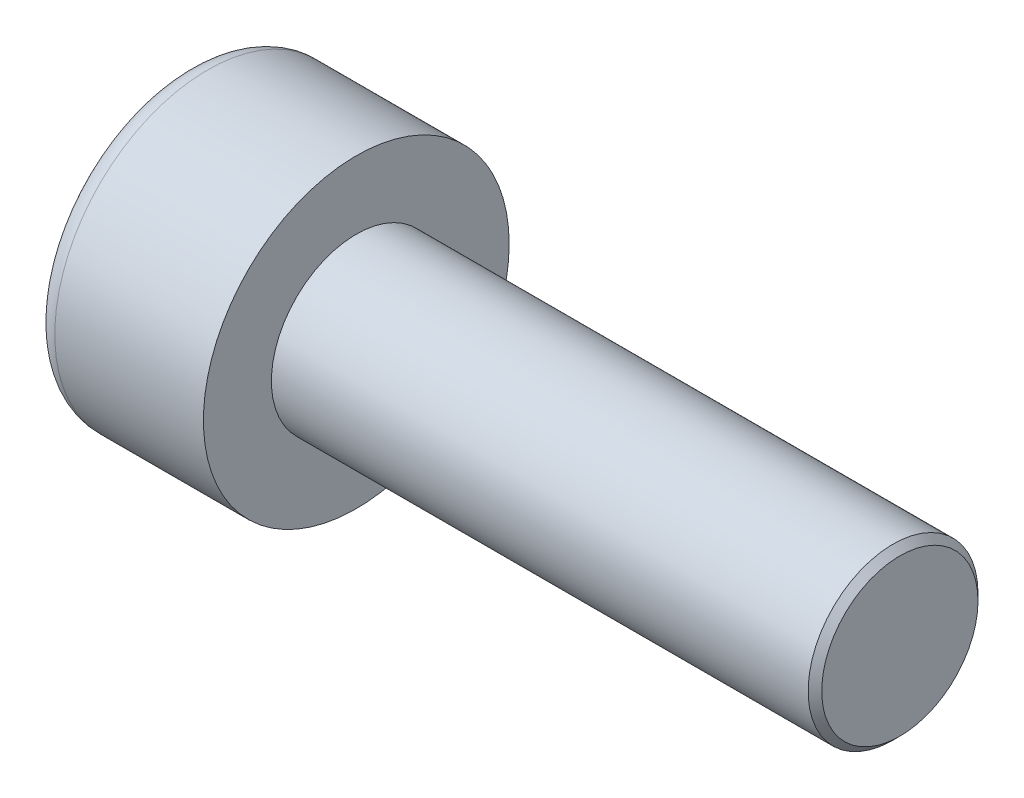
SolidWorks part; units mm, degrees
ref_plane "Front" through (0, 0, 0) normal (0, 0, 1) x (1, 0, 0)
ref_plane "Top" through (0, 0, 0) normal (0, 1, 0) x (1, 0, 0)
ref_plane "Right" through (0, 0, 0) normal (1, 0, 0) x (0, 0, -1)
sketch "Sketch1" plane through (0, 0, 0) normal (1, 0, 0) x (0, 0, -1)
  circle A0 centre (0, 0) radius 2.25
  dimension "dk" = 4.5
extrude "BaseHead" add sketch "Sketch1" along normal blind 2.5
sketch "Sketch2" plane through (2.5, 0, 0) normal (1, 0, 0) x (0, 0, -1)
  circle A0 centre (0, 0) radius 1.25
  dimension "d" = 2.5
extrude "BaseBody" add sketch "Sketch2" along normal blind 8
cosmetic thread "ThreadCosmetic1" [suppressed] parameters "b"=8, "D2"=2.013
sketch "Sketch3" plane through (0, 0, 0) normal (1, 0, 0) x (0, 0, -1)
  line L1 (1.1547, 0) -> (0.5774, 1)
  line L2 (0.5774, 1) -> (-0.5774, 1)
  line L3 (-0.5774, 1) -> (-1.1547, 0)
  line L4 (-1.1547, 0) -> (-0.5774, -1)
  line L5 (-0.5774, -1) -> (0.5774, -1)
  line L6 (0.5774, -1) -> (1.1547, 0)
  circle A0 centre (0, 0) radius 1 construction
  dimension "s" = 2
  dimension "e" = 2.3094
extrude "HexagonSocket" cut sketch "Sketch3" along normal blind 1.1
sketch "Sketch4" plane through (-4.1961, 0.75, 0) normal (0, 0, 1) x (-1, 0, 0)
  line L0 (-5.2961, 1.75) -> (-5.8735, 0.75)
  line L2 (-5.8735, 0.75) -> (-5.2961, 0.75)
  line L3 (-5.2961, 0.75) -> (-5.2961, 1.75)
  line L4 (-5.0351, 0.75) -> (0.839, 0.75) construction
  line L5 (-14.6961, 0.75) -> (-6.6961, 0.75) construction
  line L6 (-6.6961, 0.75) -> (-4.1961, 0.75) construction
  dimension "m" = 60
revolve "Cut-Revolve1" cut sketch "Sketch4" angle 360 about L4
fillet "HeadFillet" [suppressed] radius 0.1
fillet "TopFillet" radius 0.3125 1 edges at (0, 0, -2.25)
chamfer "Chamfer1" distance 0.1 angle 45 1 edges at (10.5, 0, -1.25)
sketch "Sketch5" plane through (0, 0, 0) normal (0, 0, 1) x (1, 0, 0)
  line L0 (10.4, 1.0391) -> (10.5217, 1.25)
  line L1 (10.5217, 1.25) -> (10.5217, 1.4935)
  line L2 (10.5217, 1.4935) -> (10.2782, 1.4935)
  line L3 (10.2782, 1.4935) -> (10.2782, 1.25)
  line L4 (10.2782, 1.25) -> (10.4, 1.0391)
  line L5 (0, 0) -> (7.8886, 0) construction
  line L6 (10.4, -1.25) -> (10.4, 1.25) construction
  dimension "D1" = 2.5
revolve "Cut-Revolve10" [suppressed] cut sketch "Sketch5" angle 360 about L5
pattern_linear "LPattern10" [suppressed] count 27 spacing 0.2922 along (1, 0, 0)
equation "\"r1@TopFillet\" = \"d@Sketch2\" / 8"
equation "\"D1@Chamfer1\" = \"r@HeadFillet\""
equation "\"D1@Sketch5\" = \"d@Sketch2\""
equation "\"D2@Sketch5\" =  ( \"d@Sketch2\" - \"D2@ThreadCosmetic1\" )  / 2"
equation "\"D3@LPattern10\" = \"D2@Sketch5\" * 1.2"
equation "\"D1@LPattern10\" = \"b@ThreadCosmetic1\" / \"D3@LPattern10\""
